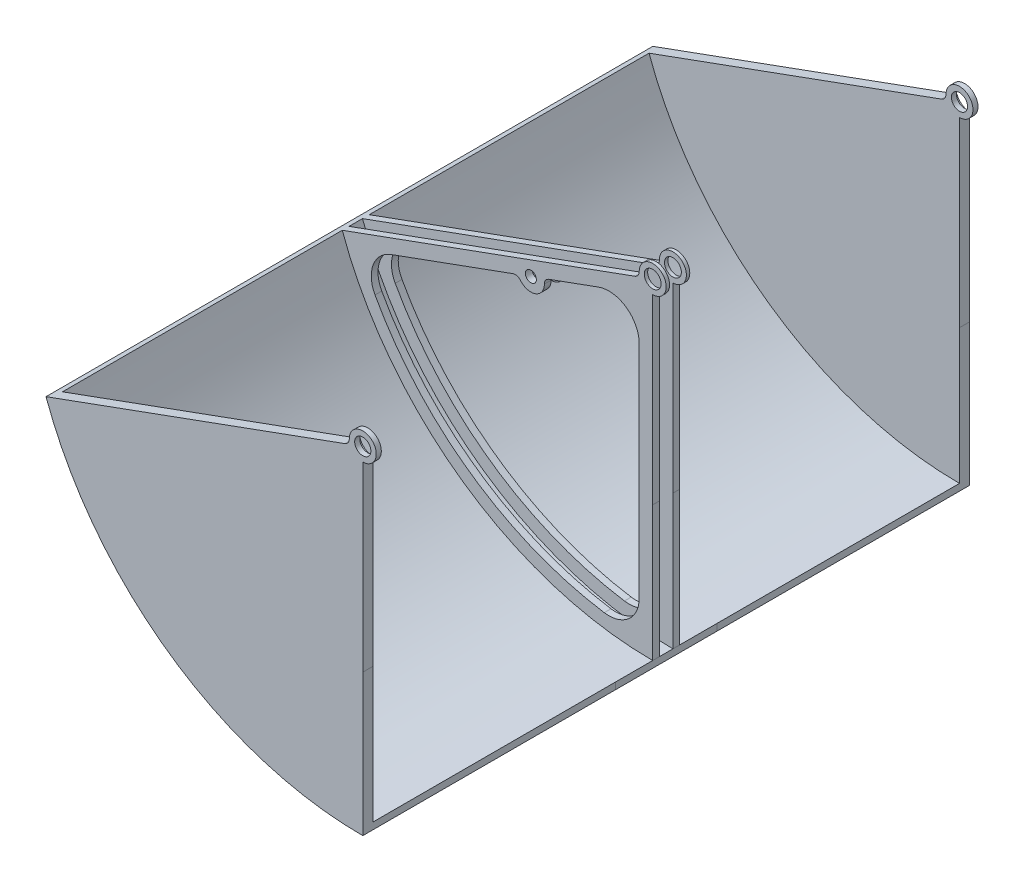
SolidWorks part; units mm, degrees
ref_plane "Płaszczyzna przednia" through (0, 0, 0) normal (0, 0, 1) x (1, 0, 0)
ref_plane "Płaszczyzna górna" through (0, 0, 0) normal (0, 1, 0) x (1, 0, 0)
ref_plane "Płaszczyzna prawa" through (0, 0, 0) normal (1, 0, 0) x (0, 0, -1)
sketch "Szkic1" plane through (0, 0, 0) normal (0, 0, 1) x (1, 0, 0)
  line L0 (-469.8463, -171.0101) -> (0, 0)
  line L1 (0, 0) -> (0, -500)
  arc A0 (0, -500) -> (-469.8463, -171.0101) centre (0, 0) cw
  dimension "D1" = 500
  dimension "D2" = 70
extrude "Dodanie-wyciągnięcie1" add sketch "Szkic1" along normal blind 900
shell "Skorupa1" thickness 10
sketch "Szkic4" plane through (0, 0, 0) normal (0, 0, -1) x (-1, 0, 0)
  line L1 (0, -20) -> (0, -490)
  line L2 (460.4494, -167.5899) -> (18.7939, -6.8404)
  arc A0 (460.4494, -167.5899) -> (0, -490) centre (0, 0) cw
  arc A1 (0, -20) -> (18.7939, -6.8404) centre (0, 0) cw
  circle A2 centre (0, 0) radius 12
  dimension "D1" = 20
  dimension "D2" = 24
extrude "Dodanie-wyciągnięcie3" add sketch "Szkic4" against normal blind 15
ref_plane "Płaszczyzna1" through (0, 0, 450) normal (0, 0, 1) x (1, 0, 0)
mirror "Lustro1" about plane through (0, 0, 450) normal (0, 0, 1) of "Dodanie-wyciągnięcie3"
ref_plane "Płaszczyzna2" through (0, 0, 440) normal (0, 0, 1) x (1, 0, 0)
sketch "Szkic6" plane through (0, 0, 440) normal (0, 0, 1) x (1, 0, 0)
  line L0 (-18.7939, -6.8404) -> (-460.4494, -167.5899)
  line L1 (0, -500) -> (0, -20) construction
  line L2 (0, -20) -> (0, -490)
  line L3 (-20, -28.563) -> (-20, -469.5743)
  line L4 (-20, -28.563) -> (-161.9042, -80.2119)
  line L5 (-199.4919, -93.8927) -> (-434.4151, -179.3977)
  line L6 (-20, -28.563) -> (-434.4151, -179.3977) construction
  arc A0 (-460.4494, -167.5899) -> (0, -490) centre (0, 0) ccw
  arc A1 (0, -20) -> (-18.7939, -6.8404) centre (0, 0) ccw
  circle A2 centre (0, 0) radius 12.5
  arc A3 (-434.4151, -179.3977) -> (-20, -469.5743) centre (0, 0) ccw
  arc A4 (-20, -28.563) -> (-20, -28.563) centre (-20, -28.563) ccw
  circle A5 centre (-180.6981, -87.0523) radius 8.15
  arc A6 (-199.4919, -93.8927) -> (-161.9042, -80.2119) centre (-180.6981, -87.0523) ccw
  dimension "D1" = 490
  dimension "D3" = 470
  dimension "D4" = 25
  dimension "D7" = 270
  dimension "D8" = 16.3
  dimension "D9" = 20
  dimension "D2" = 470
  dimension "D5" = 20
  dimension "D6" = 70
extrude "Dodanie-wyciągnięcie4" add sketch "Szkic6" against normal blind 10
mirror "Lustro6" about plane through (0, 0, 450) normal (0, 0, 1) of "Dodanie-wyciągnięcie4"
fillet "Zaokrąglenie3" radius 45 6 edges at (-20, -28.563, 435) (-20, -469.5743, 465) (-20, -469.5743, 435) (-20, -28.563, 465) (-434.4151, -179.3977, 465) (-434.4151, -179.3977, 435)
sketch "Szkic8" plane through (0, 0, 0) normal (0, 0, -1) x (-1, 0, 0)
  circle A0 centre (0, 0) radius 20
extrude "Wytnij-wyciągnięcie1" cut sketch "Szkic8" against normal blind 7.5
sketch "Szkic11" plane through (0, 0, 430) normal (0, 0, -1) x (-1, 0, 0)
  circle A1 centre (0, 0) radius 20
extrude "Wytnij-wyciągnięcie2" cut sketch "Szkic11" against normal blind 5
sketch "Szkic12" plane through (0, 0, 460) normal (0, 0, -1) x (-1, 0, 0)
  circle A0 centre (0, 0) radius 20
extrude "Wytnij-wyciągnięcie3" cut sketch "Szkic12" against normal blind 5
sketch "Szkic13" plane through (0, 0, 885) normal (0, 0, -1) x (-1, 0, 0)
  circle A0 centre (0, 0) radius 20
extrude "Wytnij-wyciągnięcie4" cut sketch "Szkic13" against normal blind 7.5
fillet "Zaokrąglenie4" radius 10 4 edges at (-18.7939, -6.8404, 11.25) (-18.7939, -6.8404, 437.5) (-18.7939, -6.8404, 467.5) (-18.7939, -6.8404, 896.25)
fillet "Zaokrąglenie5" radius 10 4 edges at (-199.4919, -93.8927, 435) (-199.4919, -93.8927, 465) (-161.9042, -80.2119, 435) (-161.9042, -80.2119, 465)
sketch "Szkic15" plane through (0, 0, 0) normal (1, 0, 0) x (0, 0, -1)
  line L0 (0, -500) -> (0, -20) construction
  line L1 (-900, -500) -> (0, -500)
  line L2 (-900, -500) -> (-900, -290)
  line L3 (-900, -290) -> (0, -290)
  line L4 (0, -500) -> (0, -290)
split line "Linia podziałowa1"
sketch "Szkic16" plane through (0, 0, 0) normal (1, 0, 0) x (0, 0, -1)
  line L0 (-885, -490) -> (-470, -490) construction
  line L1 (-525, -490) -> (-375, -490)
  line L2 (-525, -490) -> (-525, -500)
  line L3 (-525, -500) -> (-375, -500)
  line L4 (-375, -490) -> (-375, -500)
  line L5 (-900, -500) -> (0, -500) construction
  line L7 (-900, -500) -> (-525, -500) construction
  line L8 (-375, -500) -> (0, -500) construction
  dimension "D1" = 150
split line "Linia podziałowa2"
